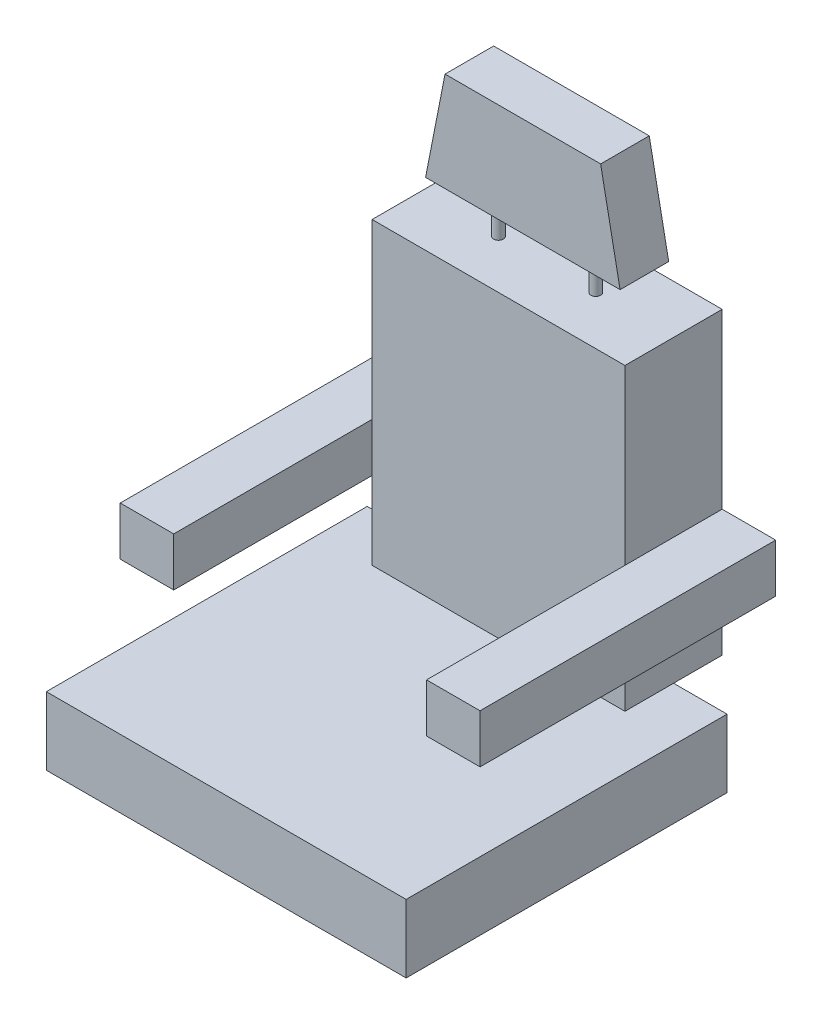
SolidWorks part; units mm, degrees
ref_plane "Front Plane" through (0, 0, 0) normal (0, 0, 1) x (1, 0, 0)
ref_plane "Top Plane" through (0, 0, 0) normal (0, 1, 0) x (1, 0, 0)
ref_plane "Right Plane" through (0, 0, 0) normal (1, 0, 0) x (0, 0, -1)
sketch "Sketch1" plane through (0, 0, 0) normal (0, 1, 0) x (1, 0, 0)
  line L1 (-234.95, 209.55) -> (234.95, 209.55)
  line L2 (-234.95, 209.55) -> (-234.95, -209.55)
  line L3 (-234.95, -209.55) -> (234.95, -209.55)
  line L4 (234.95, 209.55) -> (234.95, -209.55)
  line L5 (-234.95, 209.55) -> (234.95, -209.55) construction
  line L6 (-234.95, -209.55) -> (234.95, 209.55) construction
  point P0 (0, 0)
  dimension "D1" = 419.1
  dimension "D2" = 469.9
extrude "Boss-Extrude1" add sketch "Sketch1" along normal blind 88.9
ref_plane "Plane1" through (0, 0, -209.55) normal (0, 0, 1) x (1, 0, 0)
sketch "Sketch2" plane through (0, 0, -209.55) normal (0, 0, 1) x (1, 0, 0)
  line L1 (-165.1, 88.9) -> (165.1, 88.9)
  line L2 (-165.1, 88.9) -> (-165.1, 480.06)
  line L3 (-165.1, 480.06) -> (165.1, 480.06)
  line L4 (165.1, 88.9) -> (165.1, 480.06)
  point P5 (0, 88.9)
  dimension "D1" = 330.2
  dimension "D2" = 480.06
  dimension "D3" = 88.9
extrude "Boss-Extrude2" add sketch "Sketch2" along normal mid plane 127 separate body
sketch "Sketch3" plane through (165.1, 0, 0) normal (1, 0, 0) x (0, 0, -1)
  line L0 (273.05, 88.9) -> (273.05, 480.06) construction
  line L1 (273.05, 254) -> (-113.03, 254)
  line L2 (273.05, 254) -> (273.05, 190.5)
  line L3 (273.05, 190.5) -> (-113.03, 190.5)
  line L4 (-113.03, 254) -> (-113.03, 190.5)
  line L5 (146.05, 88.9) -> (146.05, 480.06) construction
  line L6 (-209.55, 88.9) -> (209.55, 88.9) construction
  dimension "D1" = 259.08
  dimension "D2" = 63.5
  dimension "D3" = 101.6
extrude "Boss-Extrude3" add sketch "Sketch3" along normal blind 69.85
mirror "Mirror1" about plane through (0, 0, 0) normal (1, 0, 0) of "Boss-Extrude3"
sketch "Sketch4" plane through (0, 480.06, 0) normal (0, 1, 0) x (1, 0, 0)
  line L0 (-165.1, 209.55) -> (165.1, 209.55) construction
  line L1 (-165.1, 146.05) -> (-165.1, 273.05) construction
  line L2 (165.1, 146.05) -> (165.1, 273.05) construction
  line L3 (0, 273.05) -> (0, 146.05) construction
  line L4 (165.1, 273.05) -> (-165.1, 273.05) construction
  line L5 (165.1, 146.05) -> (-165.1, 146.05) construction
  circle A0 centre (-63.5, 209.55) radius 6.35
  circle A1 centre (63.5, 209.55) radius 6.35
  dimension "D1" = 12.7
  dimension "D2" = 63.5
extrude "Boss-Extrude4" add sketch "Sketch4" along normal blind 50.8
sketch "Sketch5" plane through (0, 530.86, 0) normal (0, 1, 0) x (1, 0, 0)
  line L0 (-63.5, 209.55) -> (63.5, 209.55) construction
  line L2 (-127, 177.8) -> (127, 177.8)
  line L3 (-127, 177.8) -> (-127, 241.3)
  line L4 (-127, 241.3) -> (127, 241.3)
  line L5 (127, 177.8) -> (127, 241.3)
  line L6 (-127, 177.8) -> (127, 241.3) construction
  line L7 (-127, 241.3) -> (127, 177.8) construction
  point P4 (0, 209.55)
  dimension "D1" = 254
  dimension "D2" = 63.5
extrude "Boss-Extrude5" add sketch "Sketch5" along normal blind 129.54
sketch "Sketch6" plane through (0, 0, -177.8) normal (0, 0, 1) x (1, 0, 0)
  line L0 (-127, 530.86) -> (-101.6, 660.4)
  line L1 (0, 660.4) -> (0, 530.86) construction
  line L2 (127, 660.4) -> (127, 530.86)
  line L3 (127, 530.86) -> (101.6, 660.4)
  line L4 (-127, 530.86) -> (127, 530.86)
  line L5 (127, 530.86) -> (127, 660.4)
  line L6 (127, 660.4) -> (-127, 660.4)
  line L7 (-127, 660.4) -> (-127, 530.86)
  line L8 (-127, 530.86) -> (127, 530.86)
  line L9 (127, 530.86) -> (127, 660.4)
  line L10 (127, 660.4) -> (-127, 660.4)
  line L11 (-127, 660.4) -> (-127, 530.86)
  line M7 (127, 530.86) -> (127, 660.4)
  line M8 (127, 660.4) -> (-127, 660.4)
  line M9 (-127, 660.4) -> (-127, 530.86)
  dimension "D2" = 25.4
  dimension "D1" = 0
extrude "Cut-Extrude1" cut sketch "Sketch6" against normal blind 129.54 contours L3 M7 M8 | L0 M9 M8
